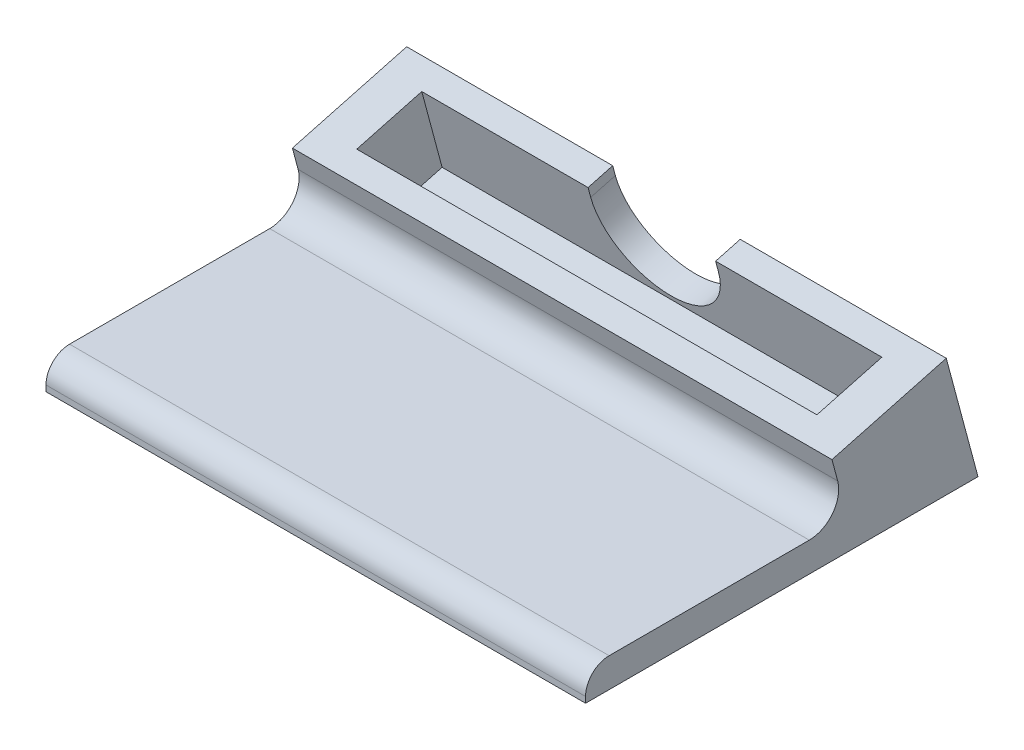
SolidWorks part; units mm, degrees
ref_plane "Front Plane" through (0, 0, 0) normal (0, 0, 1) x (1, 0, 0)
ref_plane "Top Plane" through (0, 0, 0) normal (0, 1, 0) x (1, 0, 0)
ref_plane "Right Plane" through (0, 0, 0) normal (1, 0, 0) x (0, 0, -1)
sketch "Sketch1" plane through (0, 0, 0) normal (0, 1, 0) x (1, 0, 0)
  line L1 (0, 0) -> (69.85, 0)
  line L2 (0, 0) -> (0, 50.8)
  line L3 (0, 50.8) -> (69.85, 50.8)
  line L4 (69.85, 0) -> (69.85, 50.8)
  dimension "D1" = 69.85
  dimension "D2" = 50.8
extrude "Base" add sketch "Sketch1" along normal blind 3.81
sketch "Sketch2" plane through (69.85, 0, 0) normal (1, 0, 0) x (0, 0, -1)
  line L0 (50.8, 0) -> (46.6912, 15.3341)
  line L1 (46.6912, 15.3341) -> (31.8969, 11.3699)
  line L2 (31.8969, 11.3699) -> (33.9226, 3.81)
  line L3 (0, 3.81) -> (50.8, 3.81) construction
  line L4 (50.8, 3.81) -> (50.8, 0) construction
  line L9 (0, 0) -> (50.8, 0)
  line L10 (50.8, 0) -> (50.8, 3.81)
  line L11 (50.8, 3.81) -> (0, 3.81)
  line L12 (0, 3.81) -> (0, 0)
  line L14 (50.8, 0) -> (50.8, 3.81)
  line L15 (50.8, 3.81) -> (33.9226, 3.81)
  line M3 (50.8, 3.81) -> (0, 3.81)
  dimension "D1" = 15
  dimension "D2" = 15.875
  dimension "D3" = 15.3162
  dimension "D4" = 0
extrude "Phone support" add sketch "Sketch2" against normal through all contours L1 L2 L0 M3
sketch "Sketch3" plane through (69.85, 0, 0) normal (1, 0, 0) x (0, 0, -1)
  line L0 (50.8, 0) -> (49.7791, 3.81)
  line L1 (49.7791, 3.81) -> (50.8, 3.81)
  line L2 (50.8, 3.81) -> (50.8, 0)
extrude "Front face cut" cut sketch "Sketch3" against normal through all
sketch "Sketch4" plane through (0, 2.6341, 0.7058) normal (0, 0.9659, 0.2588) x (1, 0, 0)
  line L0 (0, 43.1774) -> (5.1435, 43.1774) construction
  line L1 (5.1435, 45.767) -> (64.7065, 45.767)
  line L2 (5.1435, 45.767) -> (5.1435, 37.0548)
  line L3 (5.1435, 37.0548) -> (64.7065, 37.0548)
  line L4 (64.7065, 45.767) -> (64.7065, 37.0548)
  line L5 (0, 49.069) -> (0, 33.7528) construction
  line L6 (64.7065, 40.0907) -> (69.85, 40.0907) construction
  line L7 (69.85, 49.069) -> (69.85, 33.7528) construction
  line L8 (31.3903, 49.069) -> (31.3903, 45.767) construction
  line L9 (0, 49.069) -> (69.85, 49.069) construction
  line L10 (31.3903, 37.0548) -> (31.3903, 33.7528) construction
  line L11 (0, 33.7528) -> (69.85, 33.7528) construction
  dimension "D1" = 59.563
  dimension "D2" = 8.7122
extrude "Phone slot" cut sketch "Sketch4" against normal blind 10.16
sketch "Sketch5" plane through (0, 12.7, -47.397) normal (0, 0.2588, -0.9659) x (-1, 0, 0)
  line L0 (-34.925, -13.148) -> (-34.925, 24.9463) construction
  line L2 (-69.85, -13.148) -> (0, -13.148) construction
  line L3 (-64.7065, -7.433) -> (-5.1435, -7.433) construction
  line L5 (-43.18, 1.4062) -> (-26.67, 1.4062)
  line L6 (-43.18, 1.4062) -> (-43.18, 16.4882)
  line L7 (-43.18, 16.4882) -> (-26.67, 16.4882)
  line L8 (-26.67, 1.4062) -> (-26.67, 16.4882)
  circle A0 centre (-34.925, 1.4062) radius 8.255
  point P6 (-34.925, -13.148)
  line M4 (0, 2.727) -> (-69.85, 2.727)
  dimension "D1" = 16.51
  dimension "D2" = 8.8392
extrude "Home button hole" cut sketch "Sketch5" against normal up to next contours A0 L0 L5 | L0 A0 L5 | L0 L5 A0 M4 | L5 L0 A0 M4 | A0 L6 M4 | A0 L8 M4
fillet "Fillet1" radius 3.81 1 edges
fillet "Fillet2" radius 3.048 1 edges at (34.925, 3.81, 0)
sketch "Sketch6" plane through (0, 12.7, -47.397) normal (0, 0.2588, -0.9659) x (-1, 0, 0)
  line L0 (-68.0533, -11.5311) -> (8.7607, -11.5311) construction
  text T0 "CS" font "Century Gothic" height in points 48
extrude "Cut-Extrude4" [suppressed] cut sketch "Sketch6" against normal blind 1.27
